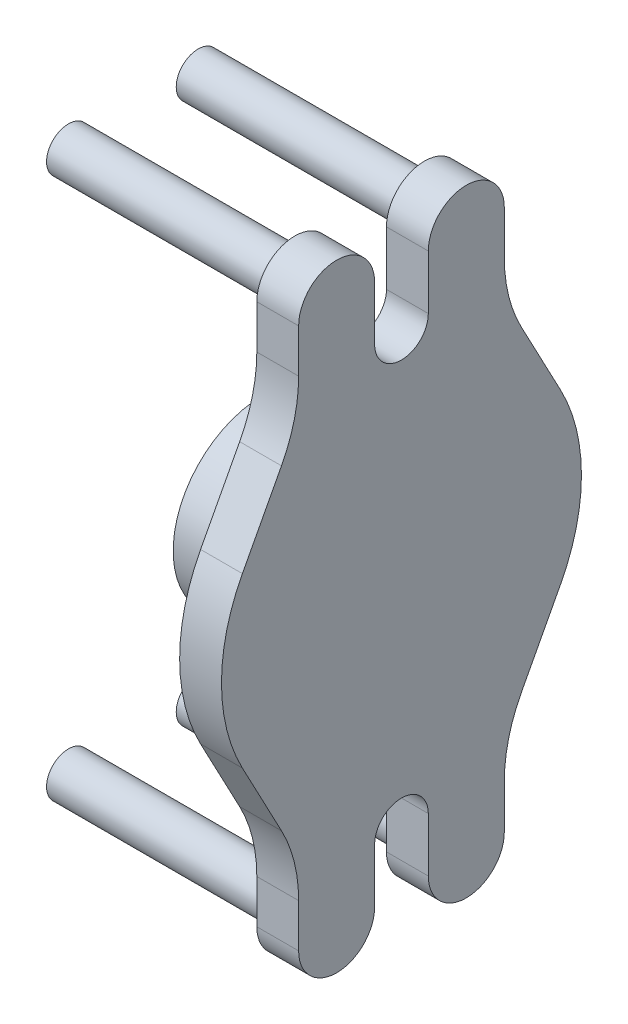
SolidWorks part; units mm, degrees
ref_plane "Front Plane" through (0, 0, 0) normal (0, 0, 1) x (1, 0, 0)
ref_plane "Top Plane" through (0, 0, 0) normal (0, 1, 0) x (1, 0, 0)
ref_plane "Right Plane" through (0, 0, 0) normal (1, 0, 0) x (0, 0, -1)
sketch "Sketch1" plane through (0, 0, 0) normal (0, 0, 1) x (1, 0, 0)
  line L0 (8.255, 0) -> (-8.255, 0) construction
  line L1 (27.9, 0) -> (-27.9, 0) construction
  line L2 (8.255, 0) -> (8.255, 18.25)
  line L3 (8.255, 18.25) -> (27.9, 18.25)
  line L4 (27.9, 18.25) -> (27.9, 0)
  line L5 (8.255, 0) -> (27.9, 0)
  point P4 (0, 0)
  point P8 (0, 0)
  dimension "D1" = 16.51
  dimension "D2" = 19.645
  dimension "D3" = 18.25
revolve "Revolve1" add sketch "Sketch1" angle 360 about L5
sketch "Sketch2" plane through (8.255, 0, 0) normal (-1, 0, 0) x (0, 0, 1)
  circle A0 centre (0, 0) radius 2.3935
  dimension "D1" = 4.787
extrude "Cut-Extrude1" cut sketch "Sketch2" against normal blind 8.5725
sketch "Sketch3" plane through (27.9, 0, 0) normal (1, 0, 0) x (0, 0, -1)
  line L0 (-20.8953, -55) -> (-20.8953, -46.1532)
  line L1 (13.175, -55) -> (-13.175, -55) construction
  line L2 (13.175, -55) -> (13.175, 55) construction
  line L3 (13.175, 55) -> (-13.175, 55) construction
  line L4 (-13.175, -55) -> (-13.175, 55) construction
  line L5 (13.175, -55) -> (-13.175, 55) construction
  line L6 (13.175, 55) -> (-13.175, -55) construction
  line L7 (-24.3823, -32.1152) -> (-32.3245, -17.1152)
  line L9 (-5.4548, -55) -> (-5.4548, -44)
  line L11 (5.4547, -44) -> (5.4547, -55)
  line L12 (20.8953, -55) -> (20.8953, -46.1532)
  line L13 (24.3823, -32.1152) -> (32.3245, -17.1152)
  line L14 (55, 0) -> (-55, 0) construction
  line L15 (13.175, -55) -> (-13.175, 55) construction
  line L16 (13.175, 55) -> (-13.175, -55) construction
  line L17 (13.175, 55) -> (-13.175, 55) construction
  line L18 (24.3823, 32.1152) -> (32.3245, 17.1152)
  line L19 (20.8953, 55) -> (20.8953, 46.1532)
  line L20 (5.4547, 44) -> (5.4547, 55)
  line L21 (-5.4548, 55) -> (-5.4548, 44)
  line L22 (-24.3823, 32.1152) -> (-32.3245, 17.1152)
  line L23 (-20.8953, 55) -> (-20.8953, 46.1532)
  arc A15 (32.3245, -17.1152) -> (32.3245, 17.1152) centre (0, 0) ccw
  arc A16 (-5.4548, 55) -> (-20.8953, 55) centre (-13.175, 55) ccw
  arc A17 (-20.8953, -55) -> (-5.4548, -55) centre (-13.175, -55) ccw
  arc A18 (5.4547, -55) -> (20.8953, -55) centre (13.175, -55) ccw
  arc A19 (20.8953, 55) -> (5.4547, 55) centre (13.175, 55) ccw
  arc A20 (-5.4548, -44) -> (5.4547, -44) centre (0, -44) cw
  arc A21 (20.8953, -46.1532) -> (24.3823, -32.1152) centre (50.8953, -46.1532) cw
  arc A22 (-20.8953, -46.1532) -> (-24.3823, -32.1152) centre (-50.8953, -46.1532) ccw
  arc A23 (-20.8953, 46.1532) -> (-24.3823, 32.1152) centre (-50.8953, 46.1532) cw
  arc A24 (20.8953, 46.1532) -> (24.3823, 32.1152) centre (50.8953, 46.1532) ccw
  arc A25 (-5.4548, 44) -> (5.4547, 44) centre (0, 44) ccw
  arc A26 (5.4547, 55) -> (20.8953, 55) centre (13.175, 55) cw
  arc A27 (-20.8953, 55) -> (-5.4548, 55) centre (-13.175, 55) cw
  arc A29 (-32.3245, 17.1152) -> (-32.3245, -17.1152) centre (0, 0) ccw
  circle M2 centre (0, 0) radius 18.25
  dimension "D3" = 15.4405
  dimension "D5" = 7.7203
  dimension "D4" = 30
  dimension "D7" = 15
  dimension "D9" = 110
  dimension "D1" = 73.152
  dimension "D6" = 15
  dimension "D2" = 26.35
  dimension "D8" = 11
extrude "Boss-Extrude1" add sketch "Sketch3" along normal blind 8.5 separate body contours L22 A29 L7 A22 L0 A17 L9 A20 L11 A18 L12 A21 L13 A15 L18 A24 L19 A19 L20 A25 L21 A16 L23 A23 M2 | M2
sketch "Sketch4" plane through (27.9, 0, 0) normal (-1, 0, 0) x (0, 0, 1)
  line L1 (13.175, -55) -> (-13.175, -55) construction
  line L2 (13.175, -55) -> (13.175, 55) construction
  line L3 (13.175, 55) -> (-13.175, 55) construction
  line L4 (-13.175, -55) -> (-13.175, 55) construction
  line L5 (13.175, -55) -> (-13.175, 55) construction
  line L6 (13.175, 55) -> (-13.175, -55) construction
  circle A0 centre (-13.175, 55) radius 4.45
  circle A1 centre (13.175, -55) radius 4.45
  circle A2 centre (13.175, 55) radius 4.45
  circle A3 centre (-13.175, -55) radius 4.45
  point P6 (0, 0)
  dimension "D1" = 8.9
extrude "Boss-Extrude2" add sketch "Sketch4" along normal blind 46
sketch "Sketch5" plane through (8.255, 0, 0) normal (-1, 0, 0) x (0, 0, 1)
  circle A0 centre (0, 0) radius 18.25
  dimension "D1" = 36.5
